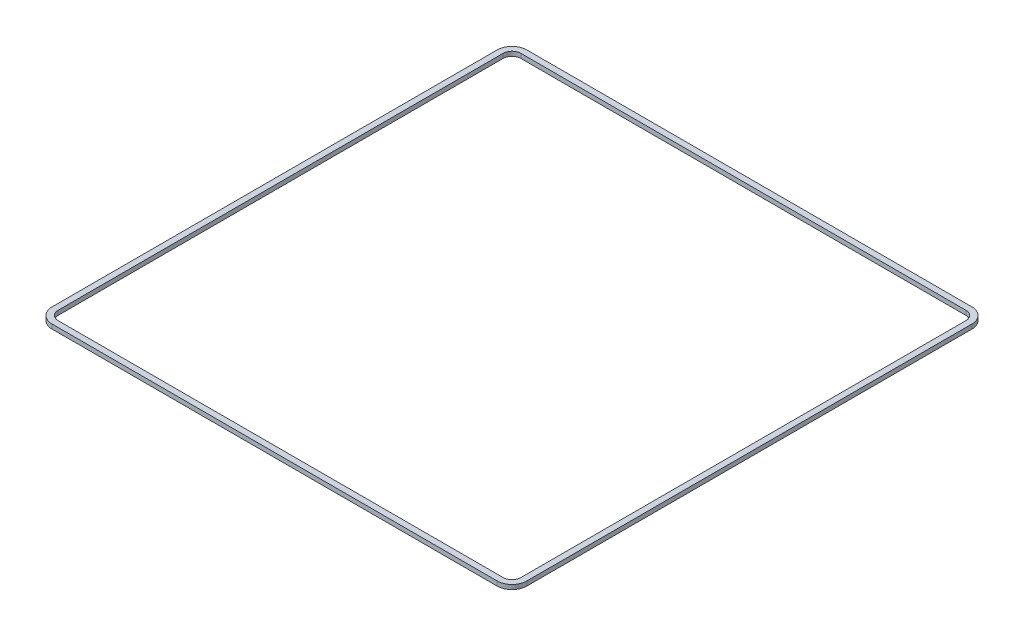
SolidWorks part; units mm, degrees
material "Cedar"
ref_plane "Front Plane" through (0, 0, 0) normal (0, 0, 1) x (1, 0, 0)
ref_plane "Top Plane" through (0, 0, 0) normal (0, 1, 0) x (1, 0, 0)
ref_plane "Right Plane" through (0, 0, 0) normal (1, 0, 0) x (0, 0, -1)
sketch "Sketch1" plane through (0, 0, 0) normal (0, 1, 0) x (1, 0, 0)
  line L0 (111.1, 83.14) -> (111.1, 84.07)
  line L1 (0, 0) -> (111.1, 0)
  line L2 (0, 0) -> (0, 83.14)
  line L3 (0, 83.14) -> (111.1, 83.14)
  line L4 (111.1, 0) -> (111.1, 83.14)
  line L5 (111.1, 0) -> (111.1, -0.93)
  line L6 (111.1, -0.93) -> (167.2, -0.93)
  line L7 (167.2, -0.93) -> (167.2, 84.07)
  line L8 (167.2, 84.07) -> (111.1, 84.07)
  line L9 (169.2, 97.57) -> (-78.8, 97.57)
  line L10 (169.2, -3.43) -> (-78.8, -3.43)
  line L11 (169.2, -14.43) -> (169.2, 97.57)
  line L12 (169.2, 86.57) -> (-78.8, 86.57)
  line L13 (-78.8, -14.43) -> (-78.8, 97.57)
  line L14 (169.2, -14.43) -> (-78.8, -14.43)
  line L16 (-114.8, 103.57) -> (205.2, 103.57)
  line L17 (-114.8, 103.57) -> (-114.8, -216.43)
  line L18 (-114.8, -216.43) -> (205.2, -216.43)
  line L19 (205.2, 103.57) -> (205.2, -216.43)
  line L20 (-54.8, -60.43) -> (145.2, -60.43)
  line L21 (-54.8, -60.43) -> (-54.8, -210.43)
  line L22 (-54.8, -210.43) -> (145.2, -210.43)
  line L23 (145.2, -60.43) -> (145.2, -210.43)
  circle A0 centre (101.6, 16) radius 1.65
  circle A1 centre (2.15, 2.15) radius 1.65
  circle A2 centre (33.15, 2.15) radius 1.65
  circle A3 centre (2.15, 53.15) radius 1.65
  circle A4 centre (57.1, 76.14) radius 1.65
  circle A5 centre (163.7, 2.57) radius 1.35
  circle A6 centre (114.7, 2.57) radius 1.35
  circle A7 centre (163.7, 60.57) radius 1.35
  circle A8 centre (114.7, 60.57) radius 1.35
  circle A9 centre (-14.3, -8.93) radius 1.65
  circle A10 centre (-66.8, -8.93) radius 1.65
  circle A11 centre (-14.3, 92.07) radius 1.65
  circle A12 centre (-66.8, 92.07) radius 1.65
  circle A13 centre (-36.05, -70.43) radius 2.25
  circle A14 centre (126.45, -70.43) radius 2.25
  circle A15 centre (128.7, -200.43) radius 2.25
  circle A16 centre (-33.8, -200.43) radius 2.25
  circle A17 centre (45.2, -135.43) radius 15
  dimension "D6" = 3.3
  dimension "D9" = 3.3
  dimension "D10" = 2
  dimension "D12" = 3.3
  dimension "D14" = 3.3
  dimension "D16" = 3.3
  dimension "D17" = 54
  dimension "D18" = 7
  dimension "D19" = 2.7
  dimension "D20" = 3.5
  dimension "D21" = 3.5
  dimension "D22" = 2.7
  dimension "D23" = 3.5
  dimension "D25" = 2.7
  dimension "D26" = 58
  dimension "D28" = 2.7
  dimension "D36" = 11
  dimension "D37" = 320
  dimension "D38" = 248
  dimension "D39" = 6
  dimension "D40" = 320
  dimension "D41" = 150
  dimension "D44" = 200
  dimension "D46" = 130
  dimension "D30" = 2
  dimension "D35" = 11
  dimension "D33" = 12
  dimension "D34" = 8
  dimension "D47" = 10
  dimension "D49" = 162.5
  dimension "D52" = 18.75
  dimension "D53" = 100
  dimension "D54" = 75
  dimension "D1" = 111.1
  dimension "D2" = 83.14
  dimension "D3" = 0.93
  dimension "D4" = 0.93
  dimension "D5" = 56.1
  dimension "D7" = 9.5
  dimension "D8" = 16
  dimension "D11" = 2.15
  dimension "D13" = 31
  dimension "D15" = 51
  dimension "D24" = 3.6
  dimension "D27" = 58
  dimension "D29" = 2
  dimension "D31" = 90
  dimension "D32" = 2.5
  dimension "D42" = 6
  dimension "D43" = 36
  dimension "D45" = 60
  dimension "D48" = 0
  dimension "D50" = 162.5
  dimension "D51" = 0
extrude "Boss-Extrude1" add sketch "Sketch1" along normal blind 3 contours L19 L16 L17 L18 L11 L14 L13 L9 L20 L23 L22 L21 | L23 L20 L21 L22 A17 A16 A15 A14 A13
fillet "Fillet1" radius 10 4 edges at (205.2, 1.5, -103.57) (-114.8, 1.5, -103.57) (205.2, 1.5, 216.43) (-114.8, 1.5, 216.43)
sketch "Sketch2" plane through (0, 3, 0) normal (0, 1, 0) x (1, 0, 0)
  line L0 (-104.8, -216.43) -> (195.2, -216.43) construction
  line L1 (205.2, 93.57) -> (205.2, -206.43) construction
  line L2 (-114.8, 93.57) -> (-114.8, -206.43) construction
  line L3 (-104.8, 103.57) -> (195.2, 103.57) construction
  line L4 (-104.8, -216.43) -> (195.2, -216.43)
  line L5 (205.2, 93.57) -> (205.2, -206.43)
  line L6 (-114.8, 93.57) -> (-114.8, -206.43)
  line L7 (-104.8, 103.57) -> (195.2, 103.57)
  line L8 (-104.8, 99.57) -> (195.2, 99.57)
  line L9 (201.2, 93.57) -> (201.2, -206.43)
  line L10 (-104.8, -212.43) -> (195.2, -212.43)
  line L11 (-110.8, 93.57) -> (-110.8, -206.43)
  arc A0 (-114.8, -206.43) -> (-104.8, -216.43) centre (-104.8, -206.43) ccw construction
  arc A1 (195.2, -216.43) -> (205.2, -206.43) centre (195.2, -206.43) ccw construction
  arc A2 (205.2, 93.57) -> (195.2, 103.57) centre (195.2, 93.57) ccw construction
  arc A3 (-104.8, 103.57) -> (-114.8, 93.57) centre (-104.8, 93.57) ccw construction
  arc A4 (-114.8, -206.43) -> (-104.8, -216.43) centre (-104.8, -206.43) ccw
  arc A5 (195.2, -216.43) -> (205.2, -206.43) centre (195.2, -206.43) ccw
  arc A6 (205.2, 93.57) -> (195.2, 103.57) centre (195.2, 93.57) ccw
  arc A7 (-104.8, 103.57) -> (-114.8, 93.57) centre (-104.8, 93.57) ccw
  arc A8 (201.2, 93.57) -> (195.2, 99.57) centre (195.2, 93.57) ccw
  arc A9 (195.2, -212.43) -> (201.2, -206.43) centre (195.2, -206.43) ccw
  arc A10 (-110.8, -206.43) -> (-104.8, -212.43) centre (-104.8, -206.43) ccw
  arc A11 (-104.8, 99.57) -> (-110.8, 93.57) centre (-104.8, 93.57) ccw
  line M10 (169.2, 97.57) -> (169.2, -14.43)
  line M11 (169.2, -14.43) -> (-78.8, -14.43)
  line M12 (-78.8, -14.43) -> (-78.8, 97.57)
  line M13 (-78.8, 97.57) -> (169.2, 97.57)
  circle M14 centre (45.2, -135.43) radius 15
  circle M15 centre (-33.8, -200.43) radius 2.25
  circle M16 centre (128.7, -200.43) radius 2.25
  circle M17 centre (126.45, -70.43) radius 2.25
  circle M18 centre (-36.05, -70.43) radius 2.25
  dimension "D1" = 4
extrude "Cut-Extrude1" cut sketch "Sketch2" against normal blind 10 contours L8 A11 L11 A10 L10 A9 L9 A8 M15 M17 M18 M16 M14 M13 M10 M11 M12
